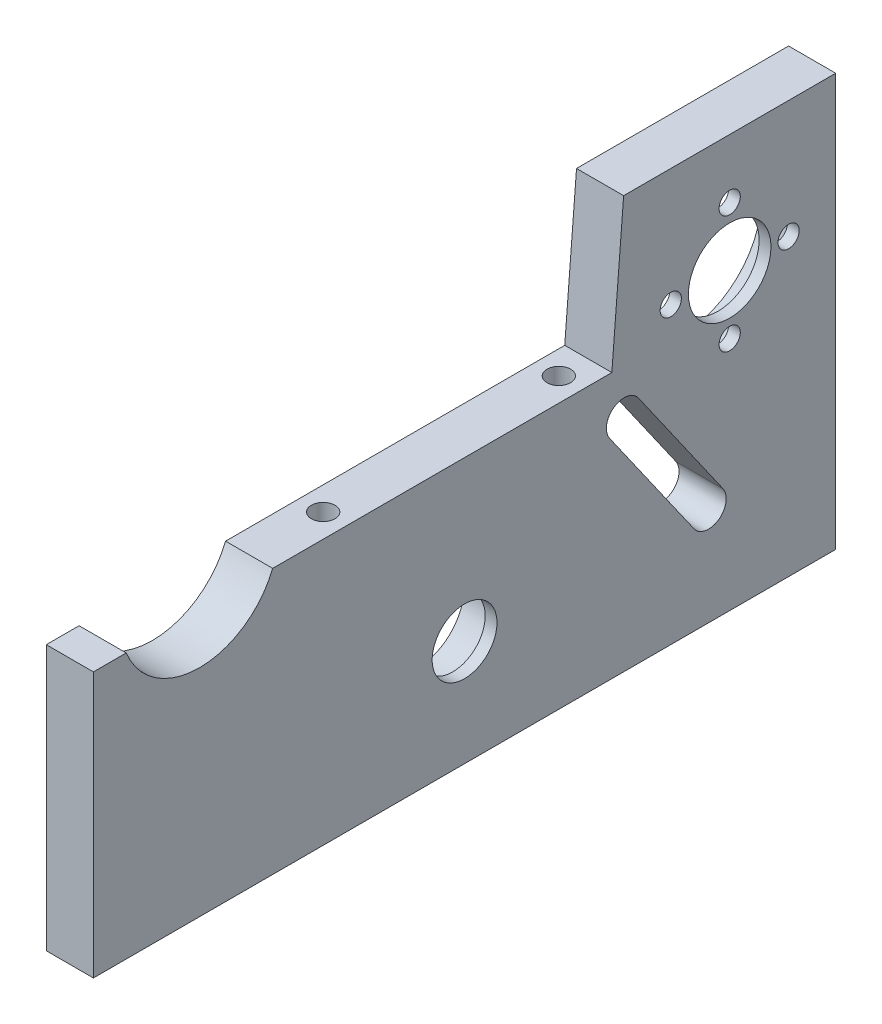
SolidWorks part; units mm, degrees
material "Alliage 1060"
ref_plane "Plan de face" through (0, 0, 0) normal (0, 0, 1) x (1, 0, 0)
ref_plane "Plan de dessus" through (0, 0, 0) normal (0, 1, 0) x (1, 0, 0)
ref_plane "Plan de droite" through (0, 0, 0) normal (1, 0, 0) x (0, 0, -1)
sketch "Esquisse2" plane through (0, 0, 0) normal (0, 1, 0) x (1, 0, 0)
  line L0 (0, 0) -> (8, 0)
  line L1 (8, 0) -> (8, 95)
  line L2 (8, 95) -> (0, 95)
  line L3 (0, 95) -> (0, 0)
  line L4 (8, 0) -> (8, 8)
  line L5 (0, 0) -> (0, -31)
  line L6 (0, -31) -> (8, -31)
  line L7 (8, -31) -> (8, 0)
extrude "Boss.-Extru.1" add sketch "Esquisse2" along normal blind 70 contours L2 L3 L0 L1 | L6 L7 L0 L5
sketch "Esquisse3" plane through (0, 0, 0) normal (-1, 0, 0) x (0, 0, 1)
  line L0 (0, 0) -> (-32, 0) construction
  line L1 (-32, 0) -> (-32, 18) construction
  line L2 (-95, 0) -> (-32, 0) construction
  circle A0 centre (-32, 18) radius 7.95
  dimension "D1" = 15.9
  dimension "D2" = 63
  dimension "D3" = 18
extrude "Enlèv. mat.-Extru.1" cut sketch "Esquisse3" against normal blind 10
sketch "Esquisse4" plane through (0, 0, 0) normal (-1, 0, 0) x (0, 0, 1)
  line L0 (0, 0) -> (-77, 0) construction
  line L1 (-95, 0) -> (31, 0) construction
  line L2 (-77, 0) -> (-77, 50) construction
  line L3 (-77, 0) -> (-31.9204, 0) construction
  line L4 (-95, 0) -> (-77, 0) construction
  circle A0 centre (-77, 50) radius 13.4
  dimension "D1" = 26.8
  dimension "D2" = 50
  dimension "D3" = 18
  dimension "D4" = 77
extrude "Enlèv. mat.-Extru.2" cut sketch "Esquisse4" against normal blind 6
sketch "Esquisse6" plane through (0, 0, 0) normal (-1, 0, 0) x (0, 0, 1)
  line L0 (-77, 50) -> (-77, 60) construction
  line L1 (-77, 50) -> (-67, 50) construction
  line L2 (-77, 50) -> (-77, 40) construction
  line L3 (-77, 50) -> (-87, 50) construction
  circle A1 centre (-77, 60) radius 1.8
  circle A2 centre (-67, 50) radius 1.8
  circle A3 centre (-77, 40) radius 1.8
  circle A4 centre (-87, 50) radius 1.8
  circle A5 centre (-77, 50) radius 7
extrude "Enlèv. mat.-Extru.3" cut sketch "Esquisse6" against normal blind 10
sketch "Esquisse7" plane through (0, 0, 0) normal (0, -1, 0) x (1, 0, 0)
  line L0 (0, 0) -> (8, 0) construction
  line L1 (8, 0) -> (8, -8) construction
  line L2 (8, 31) -> (8, -95) construction
  line L3 (8, -8) -> (0, -8) construction
  line L4 (0, -95) -> (0, 31) construction
  line L5 (0, -8) -> (0, 0) construction
  line L6 (0, 0) -> (8, -8) construction
  line L7 (8, -8) -> (8, 0) construction
  line L8 (8, 0) -> (0, -8) construction
  line L9 (0, -95) -> (8, -95) construction
  line L10 (8, -95) -> (8, -87) construction
  line L11 (8, -87) -> (0, -87) construction
  line L12 (0, -87) -> (8, -95) construction
  line L13 (8, -95) -> (0, -95) construction
  line L14 (0, -95) -> (8, -87) construction
  line L15 (0, 31) -> (8, 31) construction
  line L16 (8, 31) -> (8, 23) construction
  line L17 (8, 31) -> (8, -95) construction
  line L18 (8, 23) -> (0, 23) construction
  line L19 (0, -95) -> (0, 31) construction
  line L20 (0, 23) -> (8, 31) construction
  line L21 (8, 31) -> (0, 31) construction
  line L22 (0, 31) -> (8, 23) construction
  circle A0 centre (4, -91) radius 2
  circle A1 centre (4, -4) radius 2
  circle A2 centre (4, 27) radius 2
extrude "Enlèv. mat.-Extru.4" cut sketch "Esquisse7" against normal blind 15
sketch "Esquisse8" plane through (0, 0, 0) normal (-1, 0, 0) x (0, 0, 1)
  line L0 (-70.9529, 15.0509) -> (-56.6135, 35.5297)
  line L1 (-77, 50) -> (-59.071, 37.2505) construction
  line L2 (-59.071, 37.2505) -> (-73.4104, 16.7717) construction
  line L3 (-73.4104, 16.7717) -> (-75.8678, 18.4924) construction
  line L4 (-59.071, 37.2505) -> (-61.5284, 38.9712) construction
  line L5 (-73.4104, 16.7717) -> (-70.9529, 15.0509) construction
  line L6 (-75.8678, 18.4924) -> (-61.5284, 38.9712)
  line L7 (-59.071, 37.2505) -> (-57.1869, 35.9313)
  circle A2 centre (-73.4104, 16.7717) radius 3
  circle A5 centre (-59.071, 37.2505) radius 3
  dimension "D1" = 25
  dimension "D2" = 6
  dimension "D3" = 22
extrude "Enlèv. mat.-Extru.5" cut sketch "Esquisse8" against normal blind 10
sketch "Esquisse9" plane through (0, 0, 0) normal (-1, 0, 0) x (0, 0, 1)
  line L0 (31, 70) -> (31, 50) construction
  line L2 (31, 50) -> (13, 50) construction
  circle A0 centre (13, 50) radius 13.4
  dimension "D1" = 18
  dimension "D2" = 26.8
extrude "Enlèv. mat.-Extru.6" cut sketch "Esquisse9" against normal blind 10 contours A0
sketch "Esquisse10" plane through (0, 0, 0) normal (-1, 0, 0) x (0, 0, 1)
  line L0 (31, 0) -> (31, 45) construction
  line L1 (31, 70) -> (31, 0) construction
  line L2 (31, 45) -> (-59, 45) construction
  line L3 (-59, 45) -> (-59, 70) construction
  line L4 (-95, 70) -> (31, 70) construction
  line L5 (31, 45) -> (-57, 45)
  line L7 (-59, 70) -> (31, 70)
  line L8 (31, 70) -> (31, 45)
  line L9 (-57, 45) -> (-59, 70)
  circle M2 centre (13, 50) radius 13.4
extrude "Enlèv. mat.-Extru.7" cut sketch "Esquisse10" against normal blind 10 contours L9 L5 L8 L7 M2 | L5 M2
sketch "Esquisse11" plane through (0, 0, 0) normal (-1, 0, 0) x (0, 0, 1)
  line L0 (-77, 50) -> (-32, 18) construction
  line L1 (-77, 50) -> (-77, 0) construction
  line L2 (-95, 0) -> (31, 0) construction
  line L3 (-77, 0) -> (-32, 0) construction
  line L4 (-32, 0) -> (-32, 18) construction
  circle A0 centre (-77, 50) radius 7
  circle A1 centre (-32, 18) radius 8.1
sketch "Esquisse12" plane through (8, 0, 0) normal (1, 0, 0) x (0, 0, -1)
  circle A0 centre (32, 18) radius 8.1
  circle A1 centre (32, 18) radius 5.5
extrude "Boss.-Extru.3" add sketch "Esquisse12" against normal blind 2
sketch "Esquisse13" plane through (0, 45, 0) normal (0, 1, 0) x (1, 0, 0)
  line L0 (0, 57) -> (0, 56) construction
  line L1 (0, 57) -> (0, -0.5678) construction
  line L2 (0, 56) -> (8, 56) construction
  line L3 (8, 57) -> (8, -0.5678) construction
  line L4 (8, 56) -> (8, 8) construction
  line L5 (8, 8) -> (0, 8) construction
  line L6 (0, 8) -> (0, 16) construction
  line L7 (0, 16) -> (8, 8) construction
  line L8 (0, 16) -> (8, 16) construction
  line L9 (8, 16) -> (0, 8) construction
  line L10 (8, 56) -> (8, 48) construction
  line L11 (8, 48) -> (0, 48) construction
  line L12 (0, 48) -> (8, 56) construction
  line L13 (8, 56) -> (0, 56) construction
  line L14 (0, 56) -> (8, 48) construction
  circle A0 centre (4, 12) radius 2
  circle A1 centre (4, 52) radius 2
extrude "Enlèv. mat.-Extru.8" cut sketch "Esquisse13" against normal blind 15
